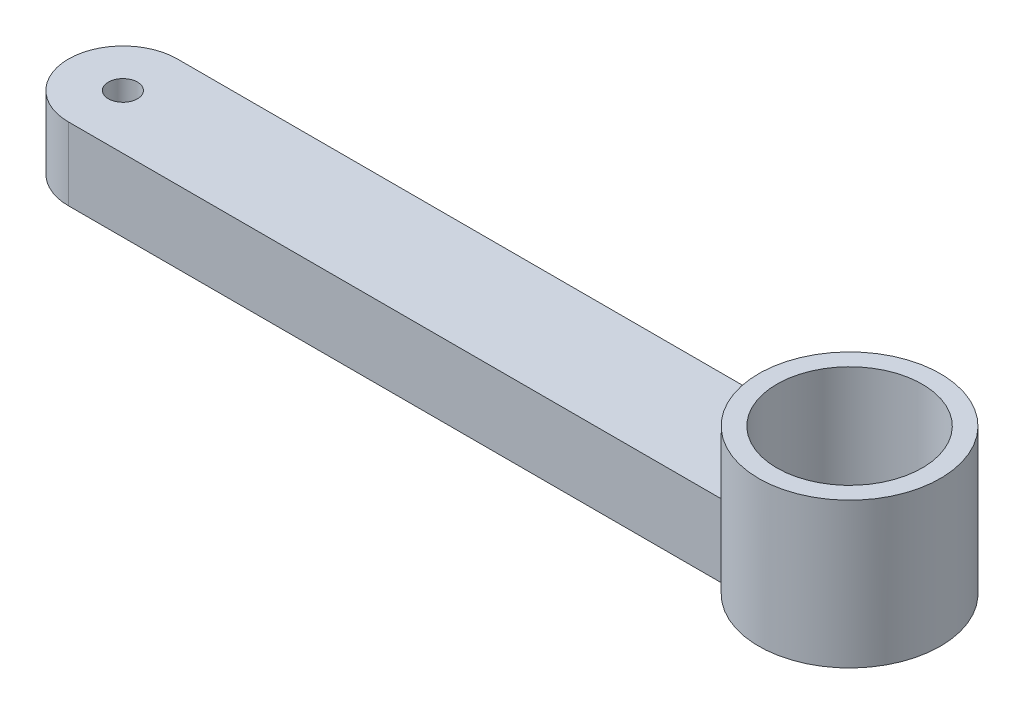
SolidWorks part; units mm, degrees
ref_plane "Front Plane" through (0, 0, 0) normal (0, 0, 1) x (1, 0, 0)
ref_plane "Top Plane" through (0, 0, 0) normal (0, 1, 0) x (1, 0, 0)
ref_plane "Right Plane" through (0, 0, 0) normal (1, 0, 0) x (0, 0, -1)
sketch "Sketch2" plane through (0, 0, 0) normal (0, 1, 0) x (1, 0, 0)
  line L0 (0, 0) -> (100, 0) construction
  line L1 (0, 7.5) -> (100, 7.5)
  line L2 (0, -7.5) -> (100, -7.5)
  arc A0 (0, 7.5) -> (0, -7.5) centre (0, 0) ccw
  arc A1 (100, -7.5) -> (100, 7.5) centre (100, 0) ccw
  circle A2 centre (0, 0) radius 2
  circle A3 centre (100, 0) radius 2.5
  point P3 (50, 0)
  dimension "D2" = 4
  dimension "D1" = 100
  dimension "D3" = 15
extrude "Boss-Extrude1" add sketch "Sketch2" along normal blind 10
sketch "Sketch3" plane through (0, 0, 0) normal (0, 1, 0) x (1, 0, 0)
  circle A0 centre (100, 0) radius 12.5
  dimension "D1" = 25
extrude "Boss-Extrude3" add sketch "Sketch3" along normal blind 20
sketch "Sketch4" plane through (0, 20, 0) normal (0, 1, 0) x (1, 0, 0)
  circle A0 centre (100, 0) radius 10
  dimension "D1" = 20
extrude "Cut-Extrude1" cut sketch "Sketch4" against normal up to next
